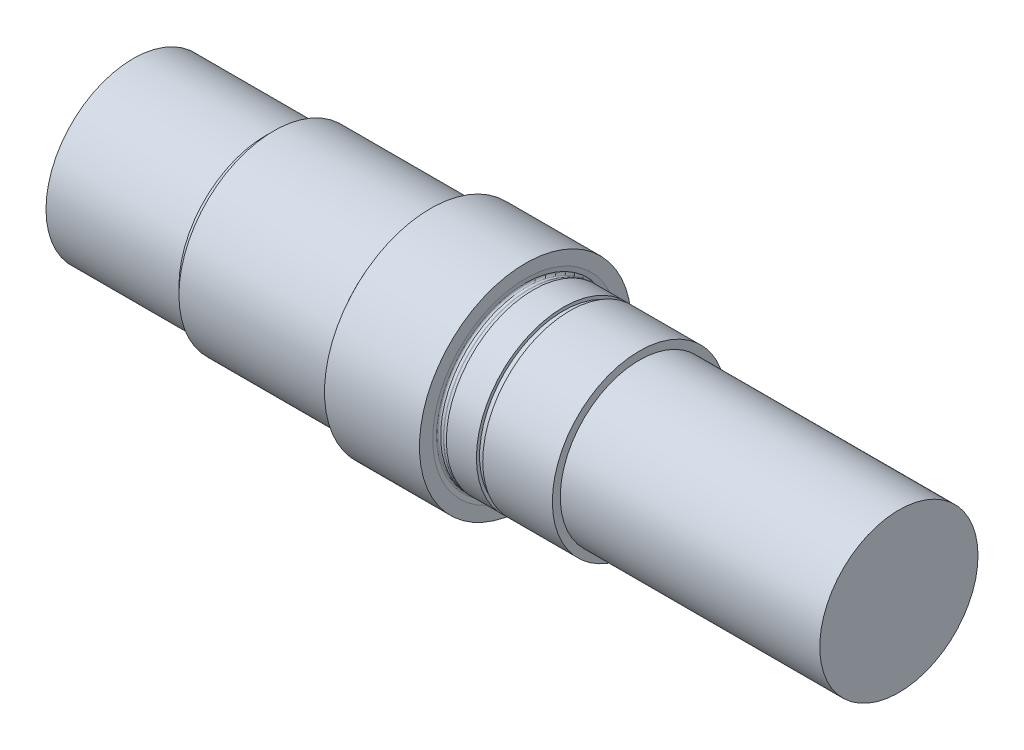
SolidWorks part; units mm, degrees
ref_plane "Ebene vorne" through (0, 0, 0) normal (0, 0, 1) x (1, 0, 0)
ref_plane "Ebene oben" through (0, 0, 0) normal (0, 1, 0) x (1, 0, 0)
ref_plane "Ebene rechts" through (0, 0, 0) normal (1, 0, 0) x (0, 0, -1)
sketch "Skizze1" plane through (0, 0, 0) normal (0, 1, 0) x (1, 0, 0)
  line L0 (0, 0) -> (339.5948, 0) construction
  line L1 (0, 0) -> (0, 27.5)
  line L2 (0, 27.5) -> (42, 27.5)
  line L3 (44.5, 30) -> (44.5, 29.3)
  line L4 (44.5, 30) -> (91.5, 30)
  line L5 (94, 31.8) -> (94, 33.5)
  line L6 (94, 33.5) -> (124, 33.5)
  line L7 (124, 33.5) -> (124, 29.3)
  line L8 (126.5, 27.5) -> (136, 27.5)
  line L9 (136, 27.5) -> (136, 26.5)
  line L10 (136, 26.5) -> (138, 26.5)
  line L11 (138, 26.5) -> (138, 27.5)
  line L12 (138, 27.5) -> (160, 27.5)
  line L13 (160, 27.5) -> (160, 25)
  line L14 (160, 25) -> (242, 25)
  line L15 (242, 25) -> (242, 0)
  line L16 (242, 0) -> (0, 0)
  line L17 (42, 27.5) -> (43.0433, 27.2204)
  line L18 (43.1986, 27.2) -> (44.0673, 27.2)
  line L19 (44.6938, 27.9207) -> (44.5, 29.3)
  line L20 (44.0673, 27.2) -> (44.7, 27.2) construction
  line L21 (44.7, 27.2) -> (44.7, 29.4742) construction
  line L22 (126.5, 27.5) -> (125.4567, 27.2204)
  line L23 (125.3014, 27.2) -> (124.4, 27.2)
  line L24 (124, 29.3) -> (123.8056, 27.8815)
  line L25 (123.8, 27.2) -> (123.8, 30) construction
  line L26 (94.2, 29.7) -> (94.2, 32.5065) construction
  line L27 (124.4, 27.2) -> (123.8, 27.2) construction
  line L28 (94, 31.8) -> (94.1944, 30.3815)
  line L29 (93.6, 29.7) -> (92.6986, 29.7)
  line L30 (92.5433, 29.7204) -> (91.5, 30)
  line L31 (93.6, 29.7) -> (94.2, 29.7) construction
  arc A0 (44.0673, 27.2) -> (44.6938, 27.9207) centre (44.0673, 27.8327) ccw
  arc A1 (124.4, 27.2) -> (123.8056, 27.8815) centre (124.4, 27.8) cw
  arc A2 (125.3014, 27.2) -> (125.4567, 27.2204) centre (125.3014, 27.8) ccw
  arc A3 (43.1986, 27.2) -> (43.0433, 27.2204) centre (43.1986, 27.8) cw
  arc A4 (94.1944, 30.3815) -> (93.6, 29.7) centre (93.6, 30.3) cw
  arc A5 (92.6986, 29.7) -> (92.5433, 29.7204) centre (92.6986, 30.3) cw
  dimension "D15" = 15
  dimension "D16" = 0.3
  dimension "D17" = 2.5
  dimension "D19" = 0.2
  dimension "D8" = 2.1
  dimension "D22" = 2.1
  dimension "D26" = 2.5
  dimension "D27" = 0.6
  dimension "D28" = 0.6
  dimension "D29" = 2.1
  dimension "D35" = 0.6
  dimension "D36" = 82
  dimension "D21" = 55
  dimension "D38" = 104
  dimension "D25" = 0.6
  dimension "D31" = 0.6
  dimension "D4" = 0.2
  dimension "D5" = 242
  dimension "D6" = 94
  dimension "D7" = 124
  dimension "D9" = 60
  dimension "D10" = 67
  dimension "D11" = 55
  dimension "D12" = 53
  dimension "D13" = 55
  dimension "D14" = 50
  dimension "D18" = 8
  dimension "D20" = 44.5
  dimension "D23" = 0.3
  dimension "D24" = 15
  dimension "D30" = 0.3
  dimension "D32" = 0.2
  dimension "D33" = 15
  dimension "D34" = 2.5
  dimension "D37" = 106
revolve "Rotation1" add sketch "Skizze1" angle 360 about L16
